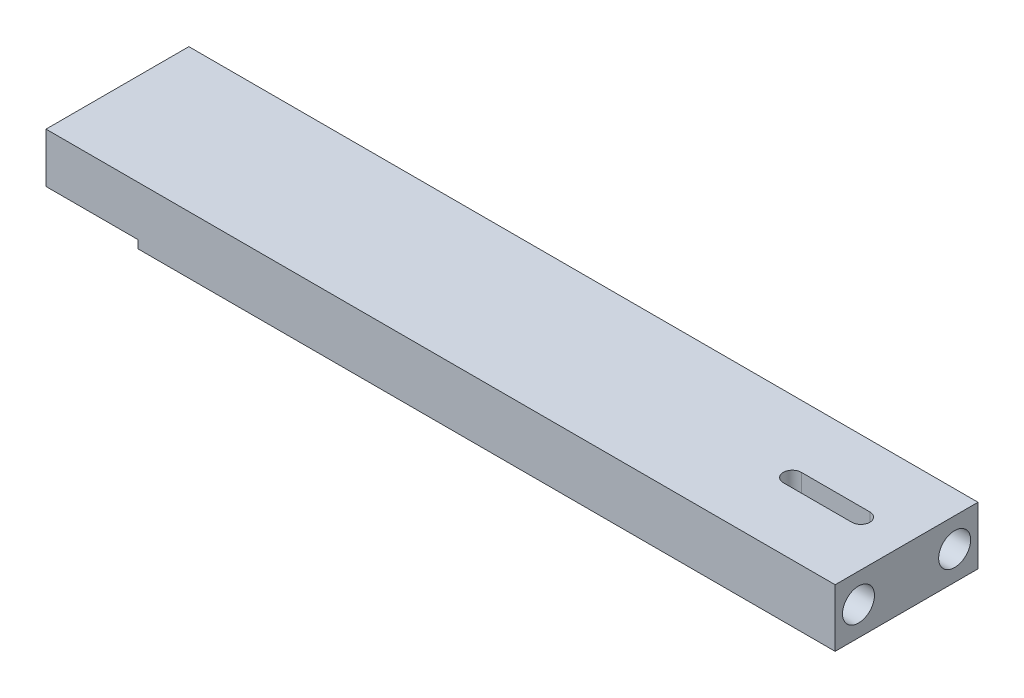
SolidWorks part; units mm, degrees
ref_plane "Alzado" through (0, 0, 0) normal (0, 0, 1) x (1, 0, 0)
ref_plane "Planta" through (0, 0, 0) normal (0, 1, 0) x (1, 0, 0)
ref_plane "Vista lateral" through (0, 0, 0) normal (1, 0, 0) x (0, 0, -1)
sketch "Croquis1" plane through (0, 0, 0) normal (0, 1, 0) x (1, 0, 0)
  line L1 (-69.75, -12.5) -> (69.75, -12.5)
  line L2 (-69.75, -12.5) -> (-69.75, 12.5)
  line L3 (-69.75, 12.5) -> (69.75, 12.5)
  line L4 (69.75, -12.5) -> (69.75, 12.5)
  line L5 (-69.75, -12.5) -> (69.75, 12.5) construction
  line L6 (-69.75, 12.5) -> (69.75, -12.5) construction
  point P0 (0, 0)
  dimension "D1" = 25
  dimension "D2" = 139.5
extrude "Saliente-Extruir1" add sketch "Croquis1" along normal blind 10.1
sketch "Croquis2" plane through (0, 0, 12.5) normal (0, 0, 1) x (1, 0, 0)
  line L0 (-69.75, 10.1) -> (-69.75, 0)
  line L1 (-69.75, 0) -> (-52.25, 0)
  line L2 (-69.75, 0) -> (69.75, 0) construction
  line L3 (-52.25, 0) -> (-52.25, 1.4)
  line L4 (-52.25, 1.4) -> (-68.35, 1.4)
  line L5 (-68.35, 1.4) -> (-68.35, 10.1)
  line L6 (-69.75, 10.1) -> (69.75, 10.1) construction
  line L7 (-68.35, 10.1) -> (-69.75, 10.1)
  dimension "D1" = 1.4
  dimension "D2" = 16.1
extrude "Cortar-Extruir1" cut sketch "Croquis2" against normal through all
sketch "Croquis3" plane through (-68.35, 0, 0) normal (-1, 0, 0) x (0, 0, 1)
  line L0 (-7.5, 5.75) -> (-12.5, 5.75) construction
  line L1 (-12.5, 1.4) -> (-12.5, 10.1) construction
  line L3 (7.5, 5.75) -> (12.5, 5.75) construction
  line L4 (12.5, 1.4) -> (12.5, 10.1) construction
  circle A0 centre (-7.5, 5.75) radius 2.675
  circle A1 centre (7.5, 5.75) radius 2.675
  dimension "D1" = 5.35
  dimension "D2" = 5
extrude "Cortar-Extruir2" cut sketch "Croquis3" against normal blind 15
sketch "Croquis4" plane through (0, 10.1, 0) normal (0, 1, 0) x (1, 0, 0)
  line L0 (61.75, 0) -> (69.75, 0) construction
  line L2 (49.75, 0) -> (61.75, 0) construction
  line L3 (49.75, 1.575) -> (61.75, 1.575)
  line L4 (49.75, -1.575) -> (61.75, -1.575)
  line L5 (69.75, -12.5) -> (69.75, 12.5) construction
  arc A1 (49.75, 1.575) -> (49.75, -1.575) centre (49.75, 0) ccw
  arc A2 (61.75, -1.575) -> (61.75, 1.575) centre (61.75, 0) ccw
  point P2 (55.75, 0)
  dimension "D1" = 1.575
  dimension "D2" = 12
  dimension "D3" = 8
extrude "Cortar-Extruir3" cut sketch "Croquis4" against normal through all
sketch "Croquis5" plane through (0, 0, 0) normal (0, -1, 0) x (1, 0, 0)
  line L0 (49.75, 1.575) -> (61.75, 1.575) construction
  line L1 (61.75, -1.575) -> (49.75, -1.575) construction
  line L2 (49.75, 1.575) -> (61.75, 1.575) construction
  line L3 (61.75, -1.575) -> (49.75, -1.575) construction
  line L4 (49.75, 4.325) -> (61.75, 4.325)
  line L5 (61.75, -4.325) -> (49.75, -4.325)
  arc A0 (49.75, 1.575) -> (49.75, -1.575) centre (49.75, 0) ccw construction
  arc A1 (61.75, -1.575) -> (61.75, 1.575) centre (61.75, 0) ccw construction
  arc A2 (49.75, 1.575) -> (49.75, -1.575) centre (49.75, 0) ccw construction
  arc A3 (61.75, -1.575) -> (61.75, 1.575) centre (61.75, 0) ccw construction
  arc A4 (61.75, -4.325) -> (61.75, 4.325) centre (61.75, 0) ccw
  arc A5 (49.75, 4.325) -> (49.75, -4.325) centre (49.75, 0) ccw
  dimension "D1" = 2.75
extrude "Cortar-Extruir4" cut sketch "Croquis5" against normal blind 5.5
fillet "Redondeo1" [suppressed] radius 10
sketch "Croquis7" plane through (69.75, 0, 0) normal (1, 0, 0) x (0, 0, -1)
  line L0 (-8.4125, 5.05) -> (-12.5, 5.05) construction
  line L1 (-12.5, 10.1) -> (-12.5, 0) construction
  line L2 (8.4125, 5.05) -> (12.5, 5.05) construction
  line L3 (12.5, 10.1) -> (12.5, 0) construction
  line L4 (-12.5, 0) -> (-4.325, 0) construction
  line L6 (-8.4125, 5.05) -> (-8.4125, 0) construction
  line L8 (-4.325, 0) -> (4.325, 0)
  line L9 (-4.325, 5.5) -> (-4.325, 0)
  line L10 (4.325, 5.5) -> (-4.325, 5.5)
  line L11 (4.325, 0) -> (4.325, 5.5)
  line L12 (-4.325, 0) -> (4.325, 0) construction
  line L13 (-4.325, 5.5) -> (-4.325, 0) construction
  line L14 (4.325, 5.5) -> (-4.325, 5.5) construction
  line L15 (4.325, 0) -> (4.325, 5.5) construction
  circle A0 centre (-8.4125, 5.05) radius 2.8
  circle A1 centre (8.4125, 5.05) radius 2.8
  dimension "D1" = 5.6
  dimension "D3" = 0
extrude "Cortar-Extruir5" cut sketch "Croquis7" against normal blind 15
